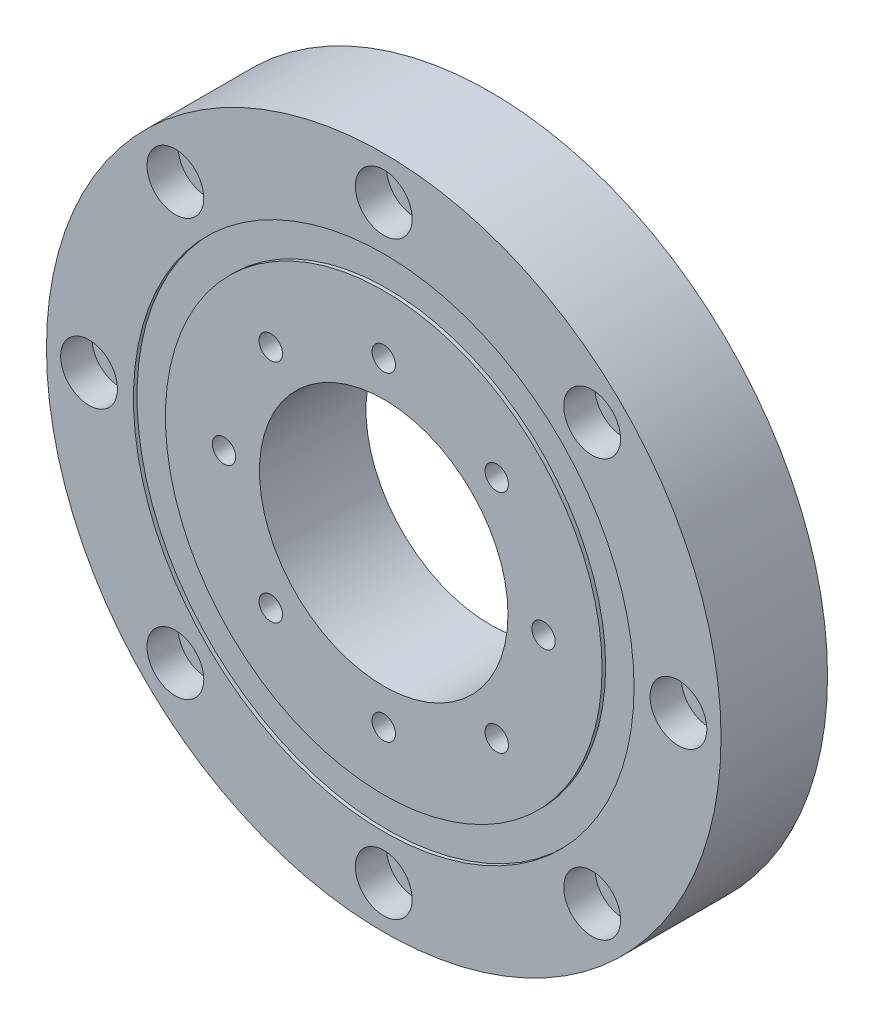
SolidWorks part; units mm, degrees
material "AISI 304"
ref_plane "前基準面" through (0, 0, 0) normal (0, 0, 1) x (1, 0, 0)
ref_plane "上基準面" through (0, 0, 0) normal (0, 1, 0) x (1, 0, 0)
ref_plane "右基準面" through (0, 0, 0) normal (1, 0, 0) x (0, 0, -1)
sketch "草圖1" plane through (0, 0, 0) normal (0, 0, 1) x (1, 0, 0)
  circle A0 centre (0, 0) radius 47.5
  dimension "D1" = 95
extrude "填料-伸長1" add sketch "草圖1" along normal mid plane 15
sketch "草圖2" plane through (0, 0, 7.5) normal (0, 0, 1) x (1, 0, 0)
  circle A0 centre (0, 0) radius 17.5
  dimension "D1" = 35
extrude "除料-伸長1" cut sketch "草圖2" against normal through all
sketch "草圖3" plane through (0, 0, 7.5) normal (0, 0, 1) x (1, 0, 0)
  circle A0 centre (0, 0) radius 30.75
  circle A1 centre (0, 0) radius 35.25
  dimension "D1" = 70.5
  dimension "D2" = 61.5
extrude "除料-伸長2" cut sketch "草圖3" against normal blind 0.5
mirror "鏡射1" about plane through (0, 0, 0) normal (0, 0, 1) of "除料-伸長2"
hole_wizard "M4 凹頭蓋螺釘的柱孔1" positions "草圖4" profile "草圖5" counterbore size "M4" standard "Ansi Metric" end condition through all
sketch "草圖4" plane through (0, 0, 7.5) normal (0, 0, 1) x (1, 0, 0)
  line L3 (0, 41.5) -> (0, -41.5) construction
  point P7 (0, 41.5)
  dimension "D1" = 83
sketch "草圖5" plane through (0, 41.5, 7.5) normal (1, 0, 0) x (0, -1, 0)
  line L0 (0, 0) -> (0, 15)
  line L1 (0, 15) -> (2.25, 15)
  line L3 (2.25, 15) -> (2.25, 4.4)
  line L4 (2.25, 4.4) -> (4, 4.4)
  line L5 (4, 4.4) -> (4, 0)
  line L7 (4, 0) -> (0, 0)
  line L11 (0, -6.35) -> (0, 107.95) construction
  dimension "貫穿孔直徑" = 4.5
  dimension "貫穿孔深度" = 15
  dimension "柱孔直徑" = 8
  dimension "柱孔深度" = 4.4
hole_wizard "M4x0.7 螺紋孔1" positions "草圖6" profile "草圖8" tap size "M4x0.7" standard "Ansi Metric" end condition through all
sketch "草圖6" plane through (0, 0, 7.5) normal (0, 0, 1) x (1, 0, 0)
  line L0 (0, -22.5) -> (0, 22.5) construction
  point P1 (0, 22.5)
  dimension "D1" = 45
sketch "草圖8" plane through (0, 22.5, 7.5) normal (1, 0, 0) x (0, -1, 0)
  line L0 (0, 0) -> (0, 15)
  line L1 (0, 15) -> (1.65, 15)
  line L2 (1.65, 15) -> (1.65, 0)
  line L5 (1.65, 0) -> (0, 0)
  line L11 (0, -6.35) -> (0, 107.95) construction
  dimension "貫穿螺孔鑽直徑" = 3.3
  dimension "貫穿螺孔鑽深度" = 15
pattern_circular "環狀複製排列1" count 8 over 360 about axis through (0, 0, 0) along (0, 0, 1) of "M4 凹頭蓋螺釘的柱孔1", "M4x0.7 螺紋孔1"
